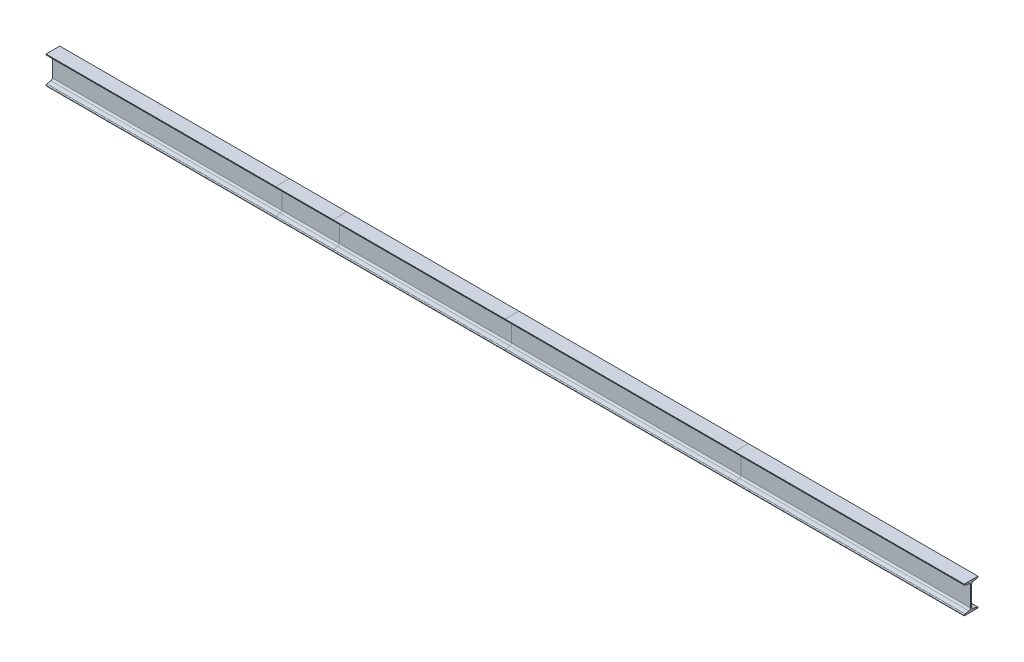
SolidWorks part; units mm, degrees
ref_plane "Front Plane" through (0, 0, 0) normal (0, 0, 1) x (1, 0, 0)
ref_plane "Top Plane" through (0, 0, 0) normal (0, 1, 0) x (1, 0, 0)
ref_plane "Right Plane" through (0, 0, 0) normal (1, 0, 0) x (0, 0, -1)
sketch "Sketch1" plane through (0, 0, 0) normal (0, 0, 1) x (1, 0, 0)
  line L0 (0, 0) -> (1000, 0)
  line L1 (1000, 0) -> (1250, 0)
  line L2 (1250, 0) -> (2000, 0)
  line L3 (2000, 0) -> (3000, 0)
  line L4 (3000, 0) -> (4000, 0)
  dimension "D1" = 1000
  dimension "D2" = 250
  dimension "D3" = 750
  dimension "D4" = 1000
  dimension "D5" = 1000
other "Sb beam - configured 120 X 12(1)"
ref_plane "Plane1" through (0, 0, 0) normal (1, 0, 0) x (0, 0, 1)
sketch "Sketch11" plane through (0, 0, 0) normal (1, 0, 0) x (0, 0, 1)
  line L0 (-30, -60) -> (-30, -58.0801)
  line L1 (-26.6576, -54.1345) -> (-9.1847, -51.2221)
  line L2 (-2.5, -43.331) -> (-2.5, 43.331)
  line L3 (-9.1847, 51.2221) -> (-26.6576, 54.1345)
  line L4 (-30, 58.0801) -> (-30, 60)
  line L5 (-30, 60) -> (30, 60)
  line L6 (30, 60) -> (30, 58.0801)
  line L7 (26.6576, 54.1345) -> (9.1847, 51.2221)
  line L8 (2.5, 43.331) -> (2.5, -43.331)
  line L9 (9.1847, -51.2221) -> (26.6576, -54.1345)
  line L10 (30, -58.0801) -> (30, -60)
  line L11 (30, -60) -> (-30, -60)
  line L15 (-2.5, 0) -> (2.5, 0) construction
  arc A0 (-9.1847, -51.2221) -> (-2.5, -43.331) centre (-10.5, -43.331) ccw
  arc A1 (-2.5, 43.331) -> (-9.1847, 51.2221) centre (-10.5, 43.331) ccw
  arc A2 (9.1847, 51.2221) -> (2.5, 43.331) centre (10.5, 43.331) ccw
  arc A3 (2.5, -43.331) -> (9.1847, -51.2221) centre (10.5, -43.331) ccw
  arc A4 (-26.6576, 54.1345) -> (-30, 58.0801) centre (-26, 58.0801) cw
  arc A5 (26.6576, 54.1345) -> (30, 58.0801) centre (26, 58.0801) ccw
  arc A6 (-30, -58.0801) -> (-26.6576, -54.1345) centre (-26, -58.0801) cw
  arc A7 (30, -58.0801) -> (26.6576, -54.1345) centre (26, -58.0801) ccw
  point P1 (0, 60)
  point P8 (0, -60)
  point P21 (0, 0)
  point P34 (0, 0)
  dimension "RI" = 8
  dimension "D3" = 4
  dimension "BF" = 60
  dimension "D2" = 9.463
  dimension "DEPTH" = 120
  dimension "TW" = 5
  dimension "D1" = 86.662
